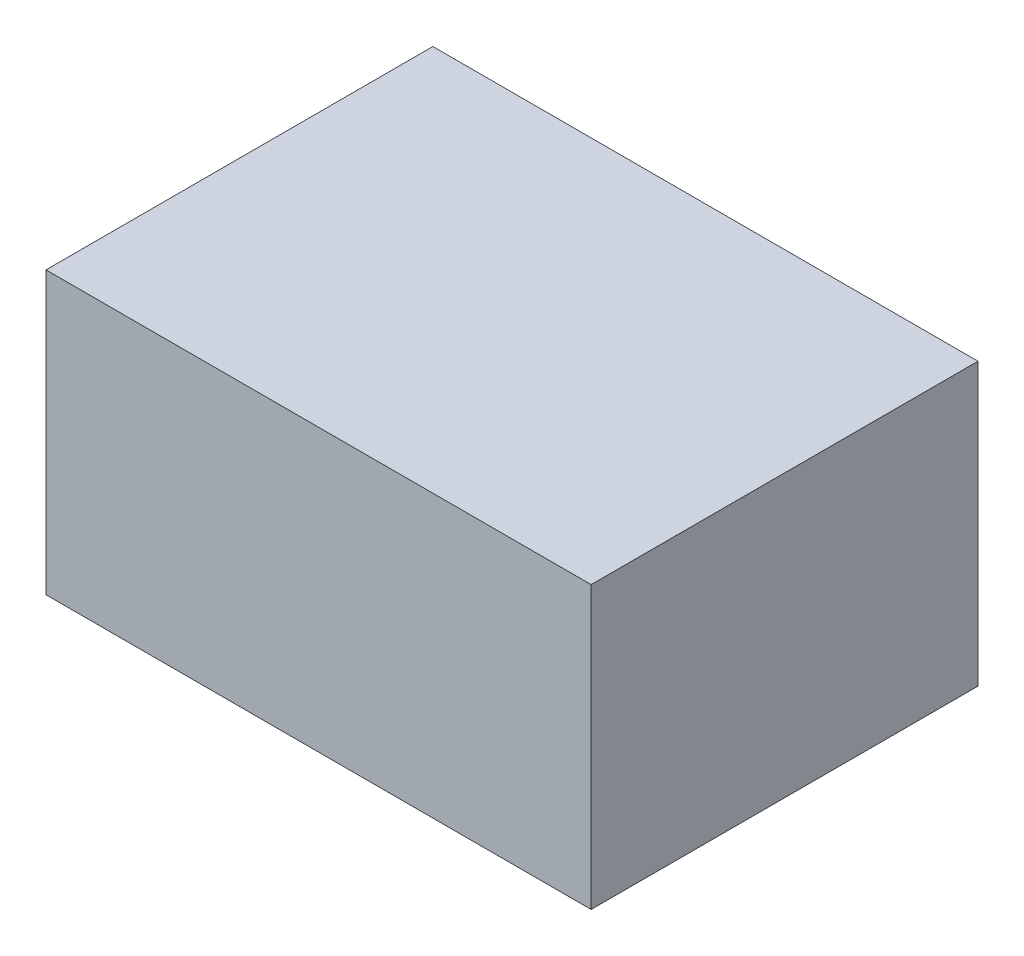
SolidWorks part; units mm, degrees
ref_plane "Front Plane" through (0, 0, 0) normal (0, 0, 1) x (1, 0, 0)
ref_plane "Top Plane" through (0, 0, 0) normal (0, 1, 0) x (1, 0, 0)
ref_plane "Right Plane" through (0, 0, 0) normal (1, 0, 0) x (0, 0, -1)
sketch "Sketch1" plane through (0, 0, 0) normal (0, 1, 0) x (1, 0, 0)
  line L1 (-59.0565, -28.5648) -> (2.9435, -28.5648)
  line L2 (-59.0565, -28.5648) -> (-59.0565, 15.4352)
  line L3 (-59.0565, 15.4352) -> (2.9435, 15.4352)
  line L4 (2.9435, -28.5648) -> (2.9435, 15.4352)
  line L5 (-59.0565, -28.5648) -> (2.9435, 15.4352) construction
  line L6 (-59.0565, 15.4352) -> (2.9435, -28.5648) construction
  point P0 (-28.0565, -6.5648)
extrude "Boss-Extrude1" add sketch "Sketch1" along normal blind 32
